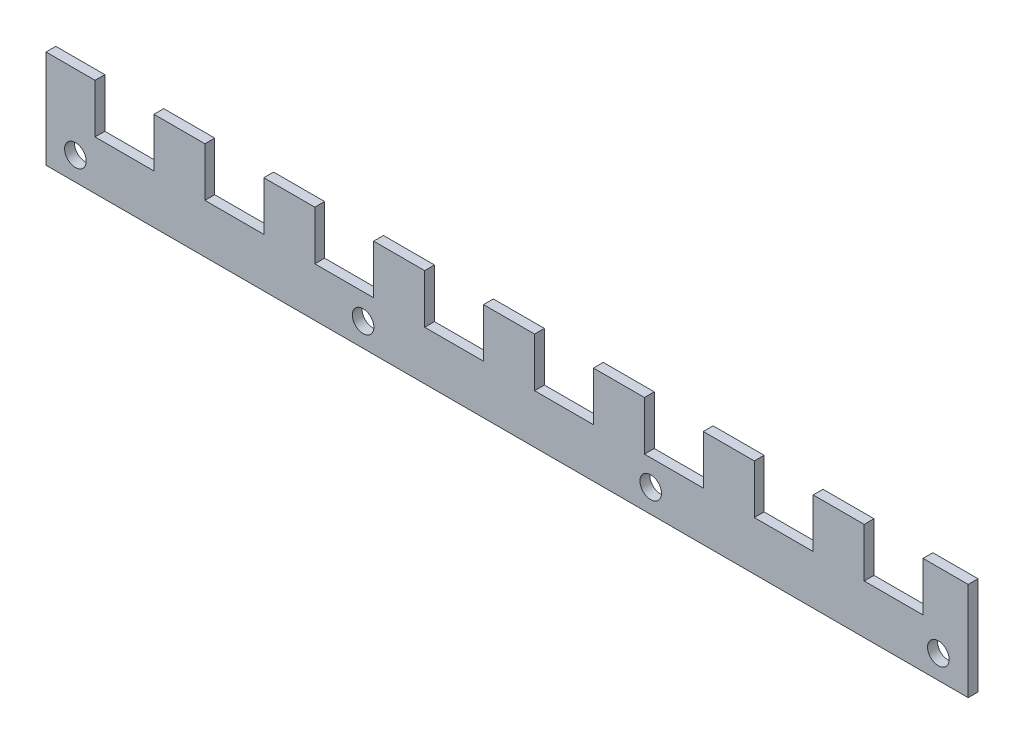
SolidWorks part; units mm, degrees
material "1.0038 (S235JRG2)"
ref_plane "Plan de face" through (0, 0, 0) normal (0, 0, 1) x (1, 0, 0)
ref_plane "Plan de dessus" through (0, 0, 0) normal (0, 1, 0) x (1, 0, 0)
ref_plane "Plan de droite" through (0, 0, 0) normal (1, 0, 0) x (0, 0, -1)
sketch "Esquisse1" plane through (0, 0, 0) normal (0, 0, 1) x (1, 0, 0)
  line L0 (-235, 0) -> (235, 0)
other "Elément mécano-soudé1"
ref_plane "Plan1" through (-235, 0, 0) normal (1, 0, 0) x (0, 1, 0)
sketch "plat" plane through (-235, 0, 0) normal (1, 0, 0) x (0, 1, 0)
  line L0 (-25, 0) -> (25, 0) construction
  line L1 (-25, 2.5) -> (25, 2.5)
  line L2 (-25, 2.5) -> (-25, -2.5)
  line L3 (-25, -2.5) -> (25, -2.5)
  line L4 (25, 2.5) -> (25, -2.5)
  line L5 (0, 2.5) -> (0, -2.5) construction
  point P8 (0, 0)
  dimension "B" = 50
  dimension "A" = 5
hole_wizard "Diamètre du perçage Ø6.2 (6.2)1" positions "Esquisse3" profile "Esquisse2" hole size "Ø6.2" standard "Ansi Metric"
sketch "Esquisse3" plane through (0, 0, 5) normal (0, 0, 1) x (1, 0, 0)
  line L0 (-235, 0) -> (235, 0) construction
  line L1 (-235, -15) -> (-235, 15) construction
  line L2 (235, 15) -> (235, -15) construction
  point P0 (-210, 0)
  point P4 (210, 0)
  point P6 (70, 0)
  point P8 (-70, 0)
  dimension "D1" = 25
  dimension "D2" = 25
  dimension "D3" = 140
  dimension "D4" = 140
sketch "Esquisse2" plane through (-210, 0, 5) normal (1, 0, 0) x (0, -1, 0)
  line L0 (0, 0) -> (0, 10)
  line L1 (0, 10) -> (3.1, 10)
  line L2 (3.1, 10) -> (3.1, 0)
  line L5 (3.1, 0) -> (0, 0)
  line L11 (0, -6.35) -> (0, 107.95) construction
  dimension "Diamètre du perçage jusqu'au prochain" = 6.2
  dimension "Profondeur du perçage jusqu'au prochain" = 10
sketch "Esquisse4" plane through (0, 0, -2.5) normal (0, 0, -1) x (-1, 0, 0)
  line L0 (-235, 25) -> (235, 25) construction
  line L1 (205, 25) -> (175, 25)
  line L2 (205, 25) -> (205, 0)
  line L3 (205, 0) -> (175, 0)
  line L4 (175, 25) -> (175, 0)
  line L5 (235, 0) -> (-235, 0) construction
  line L6 (235, -25) -> (235, 25) construction
  line L7 (105, 25) -> (105, 0)
  line L8 (105, 25) -> (75, 25)
  line L9 (105, 0) -> (75, 0)
  line L10 (75, 25) -> (75, 0)
  line L11 (5, 25) -> (5, 0)
  line L12 (5, 25) -> (-25, 25)
  line L13 (5, 0) -> (-25, 0)
  line L14 (-25, 25) -> (-25, 0)
  line L15 (-95, 25) -> (-95, 0)
  line L16 (-95, 25) -> (-125, 25)
  line L17 (-95, 0) -> (-125, 0)
  line L18 (-125, 25) -> (-125, 0)
  dimension "D1" = 30
  dimension "D2" = 30
  dimension "D3" = 4
extrude "Enlèv. mat.-Extru.1" [suppressed] cut sketch "Esquisse4" against normal through all
ref_plane "Plan2" [suppressed] through (0, 12.5, 0) normal (0, 1, 0) x (1, 0, 0)
sketch "Esquisse5" [suppressed] plane through (0, 12.5, 0) normal (0, 1, 0) x (1, 0, 0)
  line L0 (-205, 0) -> (-175.6556, -6.2374)
  line L1 (-205, -2.5) -> (-205, 2.5) construction
  line L2 (-235, 0) -> (235, 0) construction
  dimension "D1" = 30
  dimension "D2" = 12
sketch "Esquisse6" [suppressed] plane through (-205, 0, 0) normal (1, 0, 0) x (0, 0, -1)
  line L0 (-2.5, 25) -> (2.5, 25) construction
  line L1 (2.5, 0) -> (2.5, 25) construction
  line L2 (-2.5, 0) -> (-2.5, 25) construction
  line L3 (-2.5, 0) -> (2.5, 0) construction
  line L4 (-2.5, 25) -> (2.5, 25)
  line L5 (2.5, 0) -> (2.5, 25)
  line L6 (-2.5, 0) -> (-2.5, 25)
  line L7 (-2.5, 0) -> (2.5, 0)
sweep "Balayage1" [suppressed] add profiles "Esquisse6" path "Esquisse5"
pattern_linear "Répétition linéaire1" [suppressed] count 7 spacing 60
sketch "Esquisse7" plane through (0, 0, 2.5) normal (0, 0, 1) x (1, 0, 0)
  line L2 (235, 25) -> (-235, 25) construction
  line L3 (-210, 25) -> (-180, 25)
  line L4 (-210, 25) -> (-210, 0)
  line L5 (-210, 0) -> (-180, 0)
  line L6 (-180, 25) -> (-180, 0)
  line L7 (-235, -25) -> (-235, 25) construction
  dimension "D1" = 30
  dimension "D2" = 25
extrude "Enlèv. mat.-Extru.2" cut sketch "Esquisse7" against normal through all
pattern_linear "Répétition linéaire2" count 8 spacing 56 along (1, 0, 0) of "Enlèv. mat.-Extru.2"
sketch "Esquisse8" plane through (0, 0, 0) normal (0, 0, 1) x (1, 0, 0)
  line L0 (-235, -25) -> (-235, 25) construction
  line L1 (235, -25) -> (-235, -25) construction
  circle A0 centre (-220, -13) radius 5.5
  dimension "D1" = 15
  dimension "D2" = 11
  dimension "D3" = 12
extrude "Enlèv. mat.-Extru.3" cut sketch "Esquisse8" against normal mid plane 10
pattern_linear "Répétition linéaire3" count 4 spacing 146.6 along (1, 0, 0) of "Enlèv. mat.-Extru.3"
